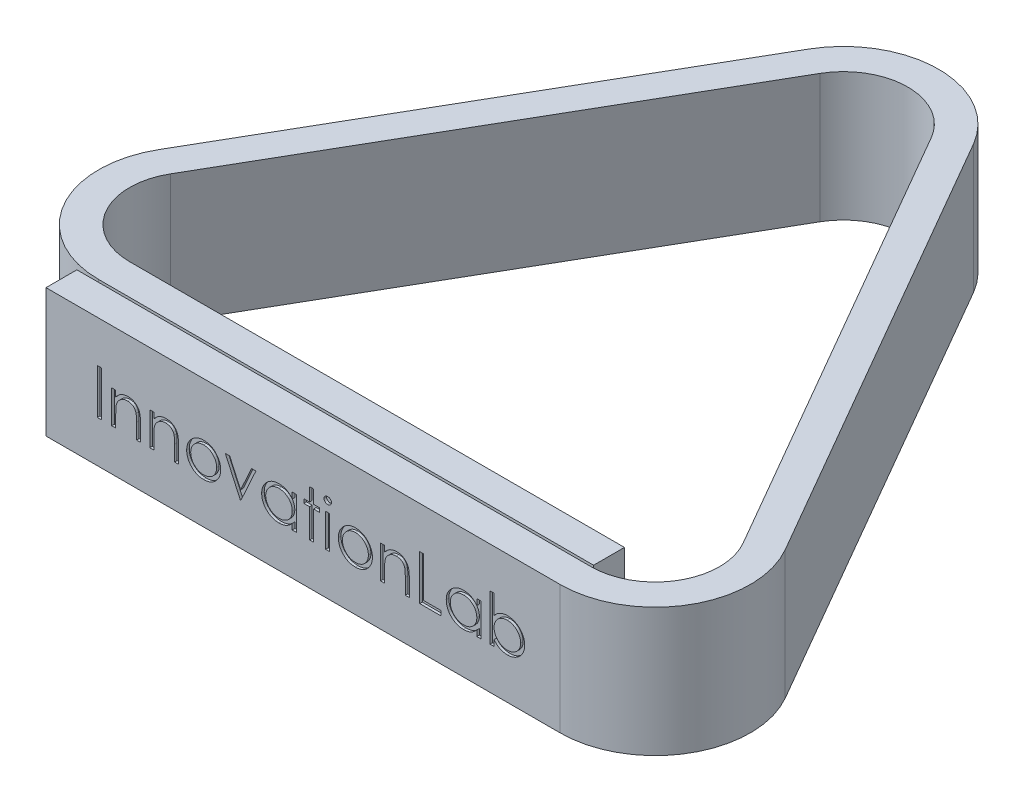
SolidWorks part; units mm, degrees
ref_plane "Plan de face" through (0, 0, 0) normal (0, 0, 1) x (1, 0, 0)
ref_plane "Plan de dessus" through (0, 0, 0) normal (0, 1, 0) x (1, 0, 0)
ref_plane "Plan de droite" through (0, 0, 0) normal (1, 0, 0) x (0, 0, -1)
sketch "Esquisse1" plane through (0, 0, 0) normal (0, 1, 0) x (1, 0, 0)
  line L0 (0, 0) -> (40, 0)
  line L1 (44.3301, 7.5) -> (24.3301, 42.141)
  line L2 (15.6699, 42.141) -> (-2.829, 10.1)
  line L3 (1.5011, 2.6) -> (40, 2.6)
  line L4 (0, -2.4) -> (40, -2.4)
  line L5 (46.4086, 8.7) -> (26.4086, 43.341)
  line L6 (13.5914, 43.341) -> (-4.9075, 11.3)
  line L7 (1.5011, 0.2) -> (40, 0.2)
  line L8 (40, 2.6) -> (40, 0.2)
  line L9 (0, 0) -> (0, -2.4)
  arc A0 (-2.829, 10.1) -> (1.5011, 2.6) centre (1.5011, 7.6) ccw
  arc A1 (40, 0) -> (44.3301, 7.5) centre (40, 5) ccw
  arc A2 (24.3301, 42.141) -> (15.6699, 42.141) centre (20, 39.641) ccw
  arc A3 (40, -2.4) -> (46.4086, 8.7) centre (40, 5) ccw
  arc A4 (26.4086, 43.341) -> (13.5914, 43.341) centre (20, 39.641) ccw
  arc A5 (-4.9075, 11.3) -> (1.5011, 0.2) centre (1.5011, 7.6) ccw
  point P25 (38.5578, 2.0993)
  dimension "D4" = 5
  dimension "D1" = 60
  dimension "D2" = 60
  dimension "D3" = 60
  dimension "D5" = 40
  dimension "D6" = 40
  dimension "D7" = 0.2
  dimension "D8" = 2.4
extrude "Boss.-Extru.1" add sketch "Esquisse1" along normal blind 10
sketch "Esquisse2" plane through (0, 0, 2.4) normal (0, 0, 1) x (1, 0, 0)
  text T0 "InnovationLab"
extrude "Enlèv. mat.-Extru.1" cut sketch "Esquisse2" against normal blind 0.2
